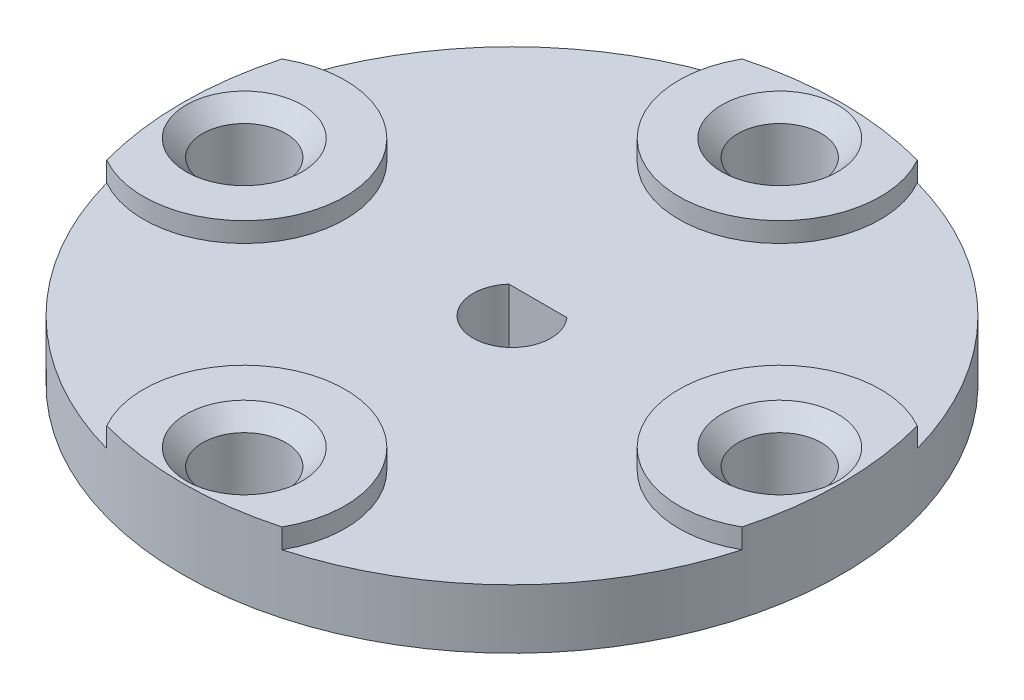
SolidWorks part; units mm, degrees
material "ABS"
ref_plane "Front Plane" through (0, 0, 0) normal (0, 0, 1) x (1, 0, 0)
ref_plane "Top Plane" through (0, 0, 0) normal (0, 1, 0) x (1, 0, 0)
ref_plane "Right Plane" through (0, 0, 0) normal (1, 0, 0) x (0, 0, -1)
sketch "Sketch1" plane through (0, 0, 0) normal (0, 1, 0) x (1, 0, 0)
  line L0 (-1.1176, 0.9984) -> (1.1176, 0.9984)
  arc A0 (-1.1176, 0.9984) -> (1.1176, 0.9984) centre (0, 0) ccw
  circle A1 centre (0, 0) radius 12.7
  dimension "D1" = 2.9972
  dimension "D2" = 25.4
  dimension "D3" = 2.2352
extrude "Boss-Extrude1" add sketch "Sketch1" along normal blind 2.286
sketch "Sketch2" plane through (0, 2.286, 0) normal (0, 1, 0) x (1, 0, 0)
  line L0 (-10.3187, 0) -> (0, 0) construction
  circle A0 centre (-10.3187, 0) radius 1.6002
  circle A1 centre (-10.3187, 0) radius 3.175 construction
  circle A2 centre (0, 0) radius 12.7 construction
  dimension "D1" = 3.2004
  dimension "D2" = 6.35
  dimension "D3" = 0.7937
extrude "Cut-Extrude1" cut sketch "Sketch2" against normal through all
pattern_circular "CirPattern1" count 4 over 360 about axis through (0, 0, 0) along (0, 1, 0) of "Cut-Extrude1"
sketch "Sketch4" plane through (0, 2.286, 0) normal (0, 1, 0) x (1, 0, 0)
  circle A0 centre (0, -10.3187) radius 1.6002 construction
  circle A1 centre (10.3187, 0) radius 1.6002 construction
  circle A2 centre (0, 10.3187) radius 1.6002 construction
  circle A3 centre (-10.3187, 0) radius 1.6002 construction
  circle A4 centre (0, -10.3187) radius 1.6002
  circle A5 centre (10.3187, 0) radius 1.6002
  circle A6 centre (0, 10.3187) radius 1.6002
  circle A7 centre (-10.3187, 0) radius 1.6002
  arc A8 (-12.243, -3.3764) -> (-12.243, 3.3764) centre (-10.3187, 0) ccw
  arc A9 (-3.3764, 12.243) -> (3.3764, 12.243) centre (0, 10.3187) ccw
  arc A10 (12.243, 3.3764) -> (12.243, -3.3764) centre (10.3187, 0) ccw
  arc A11 (3.3764, -12.243) -> (-3.3764, -12.243) centre (0, -10.3187) ccw
  circle A12 centre (0, 0) radius 12.7 construction
  arc A13 (-3.3764, -12.243) -> (3.3764, -12.243) centre (0, 0) ccw
  arc A14 (12.243, -3.3764) -> (12.243, 3.3764) centre (0, 0) ccw
  circle A15 centre (-10.3187, 0) radius 3.8862 construction
  circle A16 centre (0, -10.3187) radius 3.8862 construction
  arc A17 (3.3764, 12.243) -> (-3.3764, 12.243) centre (0, 0) ccw
  circle A18 centre (10.3187, 0) radius 3.8862 construction
  arc A19 (-12.243, 3.3764) -> (-12.243, -3.3764) centre (0, 0) ccw
  circle A20 centre (0, 10.3187) radius 3.8862 construction
  point P13 (3.8862, -10.3187)
  point P22 (14.2049, 0)
  point P23 (-6.4326, 0)
  point P32 (3.8862, 10.3187)
  dimension "D1" = 2.286
extrude "Boss-Extrude3" add sketch "Sketch4" along normal blind 0.762
chamfer "Chamfer1" distance 0.635 angle 45 4 edges at (0, 3.048, 11.9189) (10.3187, 3.048, 1.6002) (0, 3.048, -8.7186) (-10.3187, 3.048, 1.6002)
sketch "Sketch5" plane through (0, 0, 0) normal (0, -1, 0) x (1, 0, 0)
  line L0 (1.1176, -0.9984) -> (-1.1176, -0.9984) construction
  line L1 (1.1176, -0.9984) -> (-1.1176, -0.9984)
  arc A0 (1.1176, -0.9984) -> (-1.1176, -0.9984) centre (0, 0) ccw construction
  arc A1 (1.1176, -0.9984) -> (-1.1176, -0.9984) centre (0, 0) ccw
  circle A2 centre (0, 0) radius 3.0861
  dimension "D1" = 1.5875
extrude "Boss-Extrude4" add sketch "Sketch5" along normal blind 0.9525
chamfer "Chamfer2" distance 0.635 angle 45 1 edges at (0, -0.9525, -3.0861)
